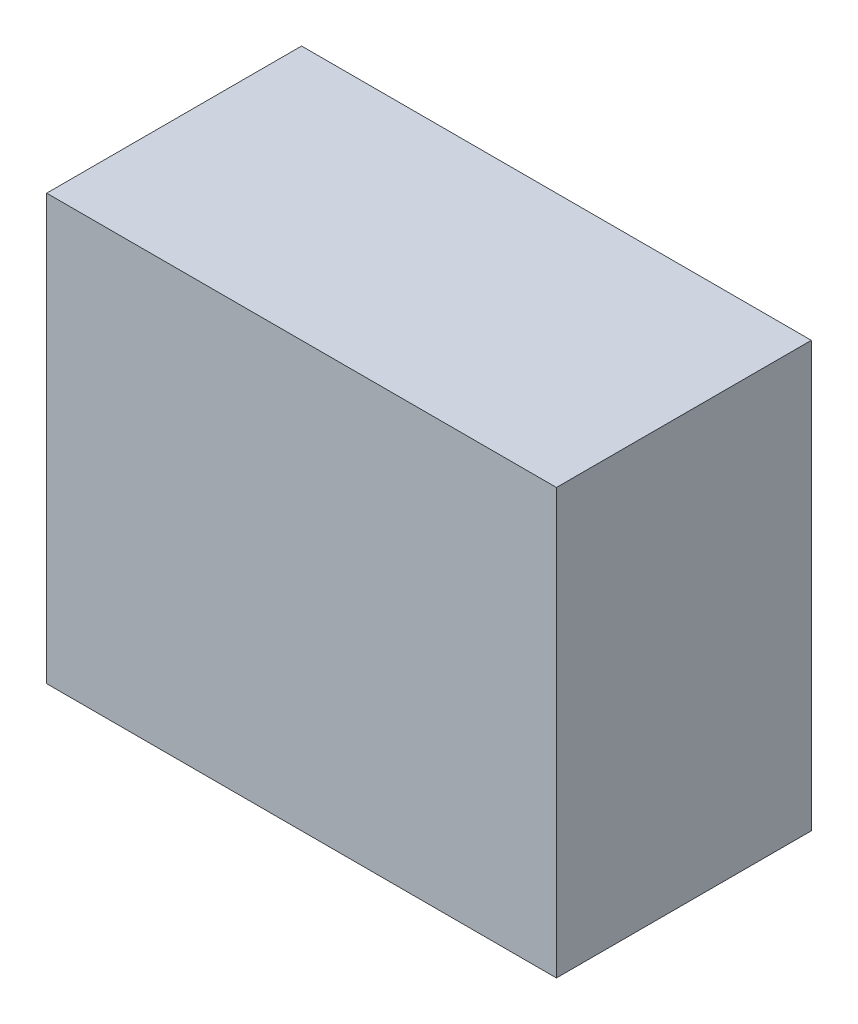
SolidWorks part; units mm, degrees
ref_plane "Front Plane" through (0, 0, 0) normal (0, 0, 1) x (1, 0, 0)
ref_plane "Top Plane" through (0, 0, 0) normal (0, 1, 0) x (1, 0, 0)
ref_plane "Right Plane" through (0, 0, 0) normal (1, 0, 0) x (0, 0, -1)
sketch "Sketch2" plane through (0, 0, 0) normal (0, 0, 1) x (1, 0, 0)
  line L1 (-15, 12.5) -> (15, 12.5)
  line L2 (-15, 12.5) -> (-15, -12.5)
  line L3 (-15, -12.5) -> (15, -12.5)
  line L4 (15, 12.5) -> (15, -12.5)
  line L5 (-15, 12.5) -> (15, -12.5) construction
  line L6 (-15, -12.5) -> (15, 12.5) construction
  point P0 (0, 0)
  dimension "D1" = 30
  dimension "D2" = 25
extrude "Boss-Extrude1" add sketch "Sketch2" along normal blind 15
